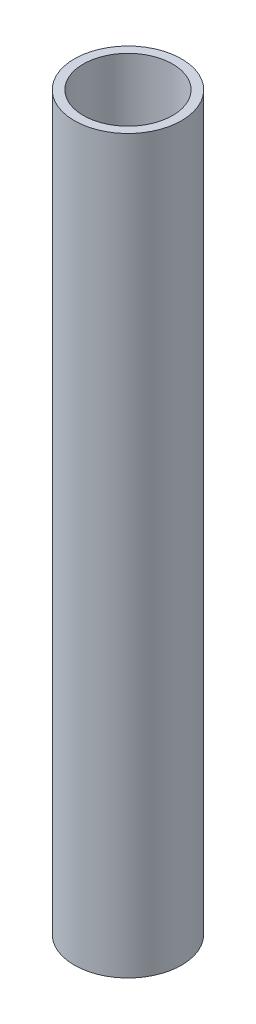
SolidWorks part; units mm, degrees
material "Plain Carbon Steel"
ref_plane "Front Plane" through (0, 0, 0) normal (0, 0, 1) x (1, 0, 0)
ref_plane "Top Plane" through (0, 0, 0) normal (0, 1, 0) x (1, 0, 0)
ref_plane "Right Plane" through (0, 0, 0) normal (1, 0, 0) x (0, 0, -1)
sketch "Sketch1" plane through (0, 0, 0) normal (0, 1, 0) x (1, 0, 0)
  circle A0 centre (0, 0) radius 9.525
  dimension "D1" = 19.05
extrude "Extrude-Thin1" add sketch "Sketch1" along normal blind 130 thin thin type one direction reverse wall 1.5875
